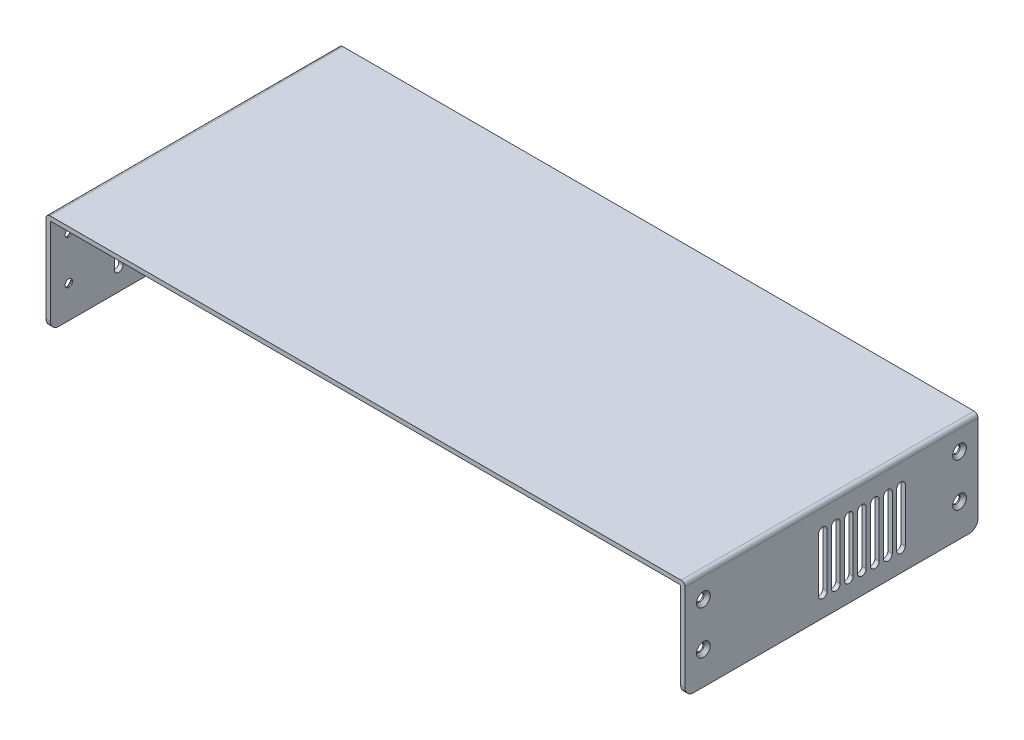
SolidWorks part; units mm, degrees
ref_plane "Front Plane" through (0, 0, 0) normal (0, 0, 1) x (1, 0, 0)
ref_plane "Top Plane" through (0, 0, 0) normal (0, 1, 0) x (1, 0, 0)
ref_plane "Right Plane" through (0, 0, 0) normal (1, 0, 0) x (0, 0, -1)
sketch "Sketch1" plane through (0, 0, 0) normal (0, 0, 1) x (1, 0, 0)
  line L0 (0, 0) -> (-2, 0)
  line L1 (-2, 0) -> (-2, 44.2)
  line L2 (-0.2, 46) -> (290.6, 46)
  line L3 (292.4, 44.2) -> (292.4, 0)
  line L4 (292.4, 0) -> (290.4, 0)
  line L5 (290.4, 0) -> (290.4, 43.5)
  line L6 (289.9, 44) -> (0.5, 44)
  line L7 (0, 43.5) -> (0, 0)
  arc A0 (290.4, 43.5) -> (289.9, 44) centre (289.9, 43.5) ccw
  arc A1 (0.5, 44) -> (0, 43.5) centre (0.5, 43.5) ccw
  arc A2 (-2, 44.2) -> (-0.2, 46) centre (-0.2, 44.2) cw
  arc A3 (290.6, 46) -> (292.4, 44.2) centre (290.6, 44.2) cw
  point P13 (0, 44)
  dimension "D5" = 0.5
  dimension "D6" = 1.8
  dimension "D1" = 44
  dimension "D2" = 290.4
  dimension "D3" = 2
  dimension "D4" = 2
extrude "Boss-Extrude1" add sketch "Sketch1" along normal blind 135
hole_wizard "CSK for M3 Flat Head Machine Screw1" positions "Sketch3" profile "Sketch2" countersink size "M3" standard "Ansi Metric"
sketch "Sketch3" plane through (-2, 0, 0) normal (-1, 0, 0) x (0, 0, 1)
  point P0 (8.5, 35)
  point P1 (8.5, 15)
  point P3 (126.5, 35)
  point P5 (126.5, 15)
sketch "Sketch2" plane through (-2, 35, 8.5) normal (0, 1, 0) x (0, 0, 1)
  line L0 (0, 0) -> (0, 6.0215)
  line L1 (0, 6.0215) -> (1.7, 5)
  line L2 (1.7, 5) -> (1.7, 1.45)
  line L3 (1.7, 1.45) -> (3.15, 0)
  line L5 (3.15, 0) -> (0, 0)
  line L6 (-1.7, 1.45) -> (-3.15, 0) construction
  line L10 (0, 6.0215) -> (-1.7, 5) construction
  line L11 (0, -6.35) -> (0, 107.95) construction
  dimension "Hole Dia." = 3.4
  dimension "Hole Depth" = 5
  dimension "Near C'Sink Dia." = 6.3
  dimension "Near C'Sink Angle" = 90
  dimension "Drill Angle" = 118
hole_wizard "CSK for M3 Flat Head Machine Screw2" positions "Sketch5" profile "Sketch4" countersink size "M3" standard "Ansi Metric"
sketch "Sketch5" plane through (292.4, 0, 0) normal (1, 0, 0) x (0, 0, -1)
  point P0 (-126.5, 35)
  point P1 (-126.5, 15)
  point P3 (-8.5, 35)
  point P5 (-8.5, 15)
sketch "Sketch4" plane through (292.4, 35, 126.5) normal (0, 1, 0) x (0, 0, -1)
  line L0 (0, 0) -> (0, 6.0215)
  line L1 (0, 6.0215) -> (1.7, 5)
  line L2 (1.7, 5) -> (1.7, 1.45)
  line L3 (1.7, 1.45) -> (3.15, 0)
  line L5 (3.15, 0) -> (0, 0)
  line L6 (-1.7, 1.45) -> (-3.15, 0) construction
  line L10 (0, 6.0215) -> (-1.7, 5) construction
  line L11 (0, -6.35) -> (0, 107.95) construction
  dimension "Hole Dia." = 3.4
  dimension "Hole Depth" = 5
  dimension "Near C'Sink Dia." = 6.3
  dimension "Near C'Sink Angle" = 90
  dimension "Drill Angle" = 118
fillet "Fillet1" radius 4 4 edges at (291.4, 0, 135) (291.4, 0, 0) (-1, 0, 135) (-1, 0, 0)
sketch "Sketch6" plane through (-2, 0, 0) normal (1, 0, 0) x (0, 0, -1)
  line L0 (-103.5, 34.375) -> (-103.5, 9.8) construction
  line L1 (-101.5, 34.375) -> (-101.5, 9.8)
  line L2 (-105.5, 34.375) -> (-105.5, 9.8)
  line L3 (-135, 4) -> (-135, 44.2) construction
  line L4 (-135, 46) -> (0, 46) construction
  arc A0 (-101.5, 34.375) -> (-105.5, 34.375) centre (-103.5, 34.375) ccw
  arc A1 (-105.5, 9.8) -> (-101.5, 9.8) centre (-103.5, 9.8) ccw
  point P2 (-103.5, 22.0875)
  dimension "D3" = 28.575
  dimension "D1" = 4
  dimension "D2" = 31.5
  dimension "D4" = 36.2
extrude "Cut-Extrude1" cut sketch "Sketch6" along normal blind 10
pattern_linear "LPattern1" count 13 spacing 6 along (0, 0, -1) of "Cut-Extrude1"
sketch "Sketch7" plane through (292.4, 0, 0) normal (1, 0, 0) x (0, 0, -1)
  line L0 (-35.5, 34.375) -> (-35.5, 9.8) construction
  line L1 (-33.5, 34.375) -> (-33.5, 9.8)
  line L2 (-37.5, 34.375) -> (-37.5, 9.8)
  line L3 (0, 4) -> (0, 44.2) construction
  line L4 (-135, 46) -> (0, 46) construction
  arc A0 (-33.5, 34.375) -> (-37.5, 34.375) centre (-35.5, 34.375) ccw
  arc A1 (-37.5, 9.8) -> (-33.5, 9.8) centre (-35.5, 9.8) ccw
  point P2 (-35.5, 22.0875)
  dimension "D2" = 36.2
  dimension "D3" = 28.575
  dimension "D1" = 35.5
  dimension "D4" = 4
extrude "Cut-Extrude2" cut sketch "Sketch7" against normal blind 10
pattern_linear "LPattern2" count 7 spacing 6 along (0, 0, 1) of "Cut-Extrude2"
